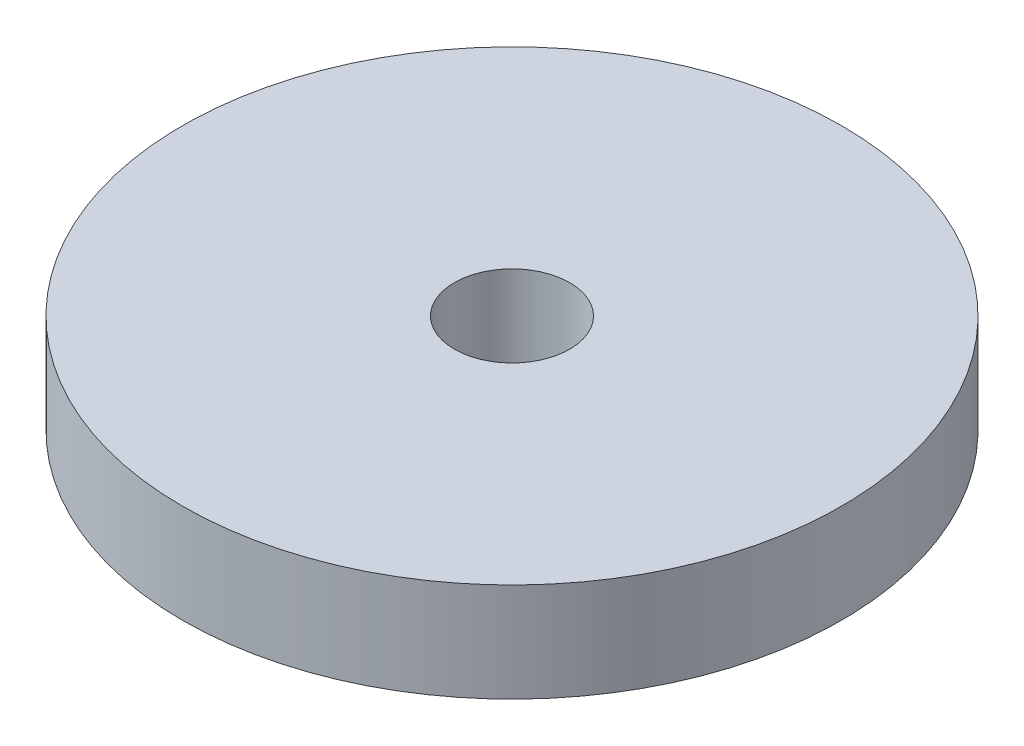
SolidWorks part; units mm, degrees
material "PE Low Density Film"
ref_plane "Front Plane" through (0, 0, 0) normal (0, 0, 1) x (1, 0, 0)
ref_plane "Top Plane" through (0, 0, 0) normal (0, 1, 0) x (1, 0, 0)
ref_plane "Right Plane" through (0, 0, 0) normal (1, 0, 0) x (0, 0, -1)
sketch "Sketch1" plane through (0, 0, 0) normal (0, 1, 0) x (1, 0, 0)
  circle A0 centre (0, 0) radius 20
  circle A1 centre (0, 0) radius 3.5
  dimension "D1" = 7
  dimension "D2" = 40
extrude "Boss-Extrude1" add sketch "Sketch1" along normal blind 6
